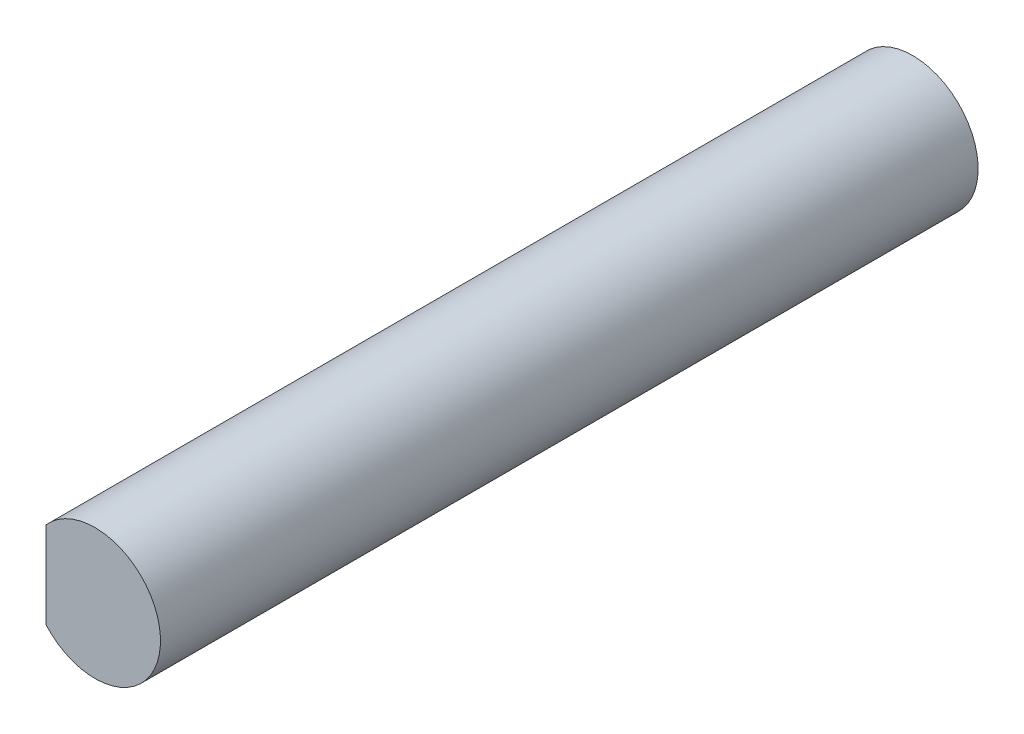
SolidWorks part; units mm, degrees
ref_plane "Front Plane" through (0, 0, 0) normal (0, 0, 1) x (1, 0, 0)
ref_plane "Top Plane" through (0, 0, 0) normal (0, 1, 0) x (1, 0, 0)
ref_plane "Right Plane" through (0, 0, 0) normal (1, 0, 0) x (0, 0, -1)
sketch "Sketch1" plane through (0, 0, 0) normal (0, 0, 1) x (1, 0, 0)
  line L0 (0, 0) -> (-1.5, 0) construction
  line L1 (-1.5, 1.3229) -> (-1.5, -1.3229)
  arc A0 (-1.5, 1.3229) -> (-1.5, -1.3229) centre (0, 0) cw
  dimension "D2" = 2
  dimension "D1" = 1.5
extrude "Boss-Extrude1" add sketch "Sketch1" along normal blind 25
